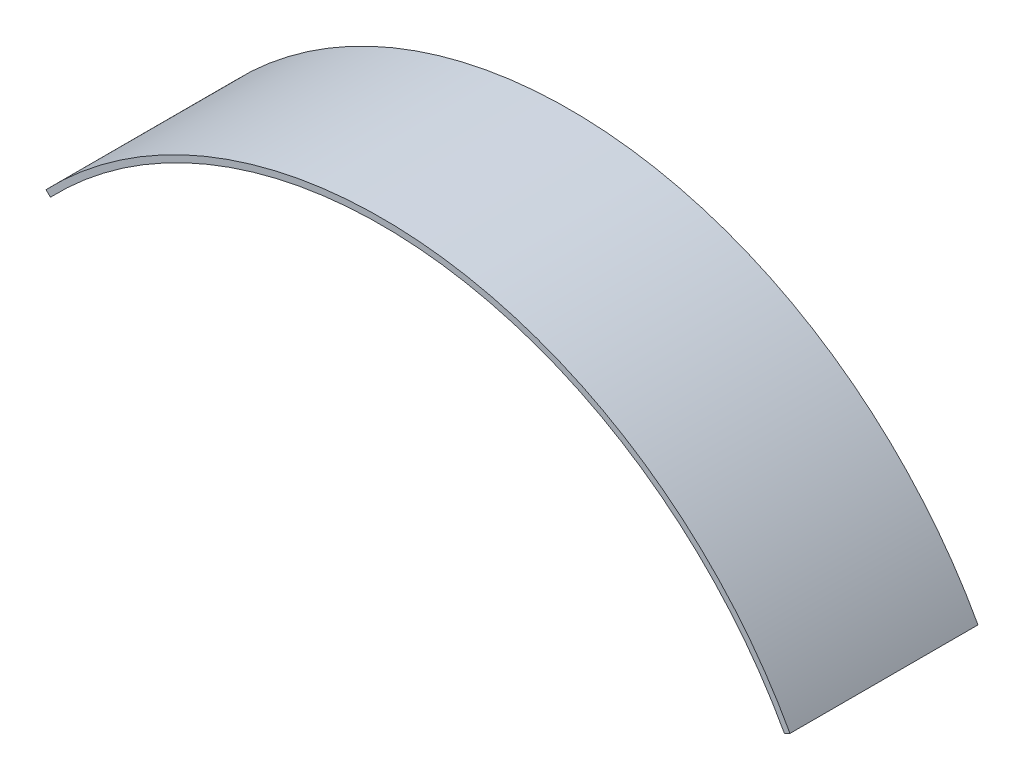
SolidWorks part; units mm, degrees
ref_plane "Front Plane" through (0, 0, 0) normal (0, 0, 1) x (1, 0, 0)
ref_plane "Top Plane" through (0, 0, 0) normal (0, 1, 0) x (1, 0, 0)
ref_plane "Right Plane" through (0, 0, 0) normal (1, 0, 0) x (0, 0, -1)
sketch "Sketch1" plane through (0, 0, 0) normal (0, 0, 1) x (1, 0, 0)
  line L0 (0, 0) -> (1.2637, -1.2106)
  line L1 (209.7099, -27.8852) -> (208.1738, -28.7235)
  arc A0 (0, 0) -> (209.7099, -27.8852) centre (94.6519, -90.6742) cw
  arc A1 (1.2637, -1.2106) -> (208.1738, -28.7235) centre (94.6519, -90.6742) cw
  dimension "D2" = 129.3256
  dimension "D3" = 208.7313
  dimension "D4" = 27.5129
  dimension "D1" = 1.75
extrude "Boss-Extrude1" add sketch "Sketch1" along normal blind 53
